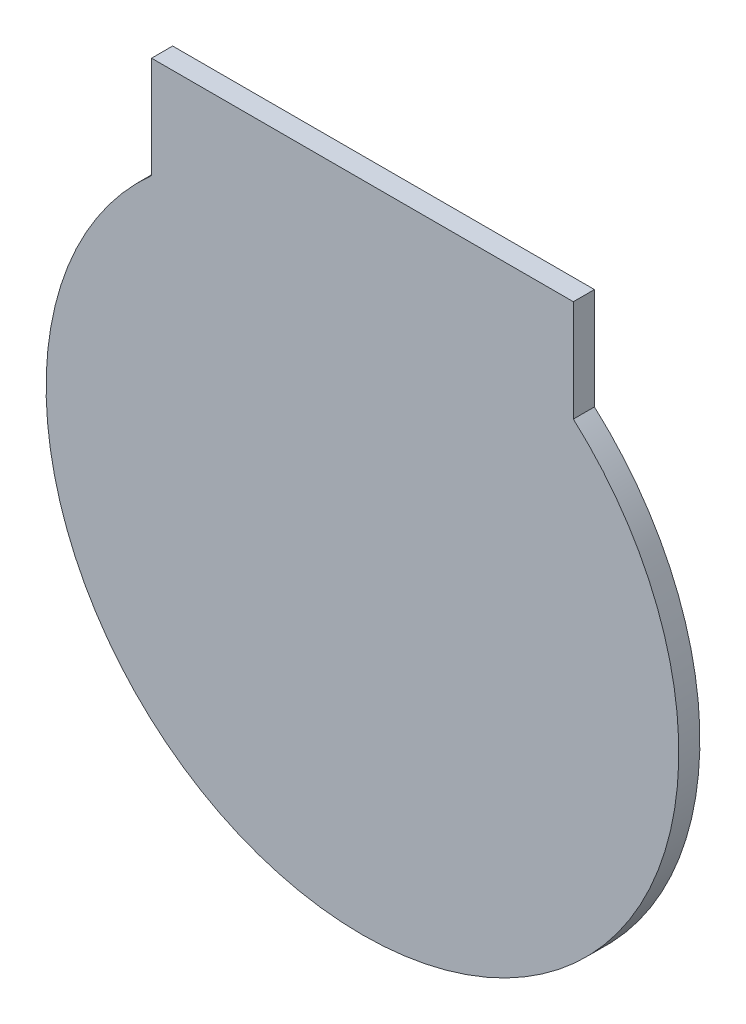
SolidWorks part; units mm, degrees
material "Acrílico (médio-alto impacto)"
ref_plane "Plano frontal" through (0, 0, 0) normal (0, 0, 1) x (1, 0, 0)
ref_plane "Plano superior" through (0, 0, 0) normal (0, 1, 0) x (1, 0, 0)
ref_plane "Plano direito" through (0, 0, 0) normal (1, 0, 0) x (0, 0, -1)
sketch "Esboço1" plane through (0, 0, 0) normal (0, 0, 1) x (1, 0, 0)
  line L2 (-55.5046, -168.4305) -> (-55.5046, -144.3322)
  line L3 (-55.5046, -144.3322) -> (44.4954, -144.3322)
  line L4 (44.4954, -168.4305) -> (44.4954, -144.3322)
  arc A0 (-55.5046, -168.4305) -> (44.4954, -168.4305) centre (-5.5046, -224.3322) ccw
  point P6 (-55.5046, -156.3813)
  dimension "D1" = 150
  dimension "D3" = 50
  dimension "D4" = 50
  dimension "D5" = 80
extrude "Ressalto-extrusão1" add sketch "Esboço1" along normal blind 5
